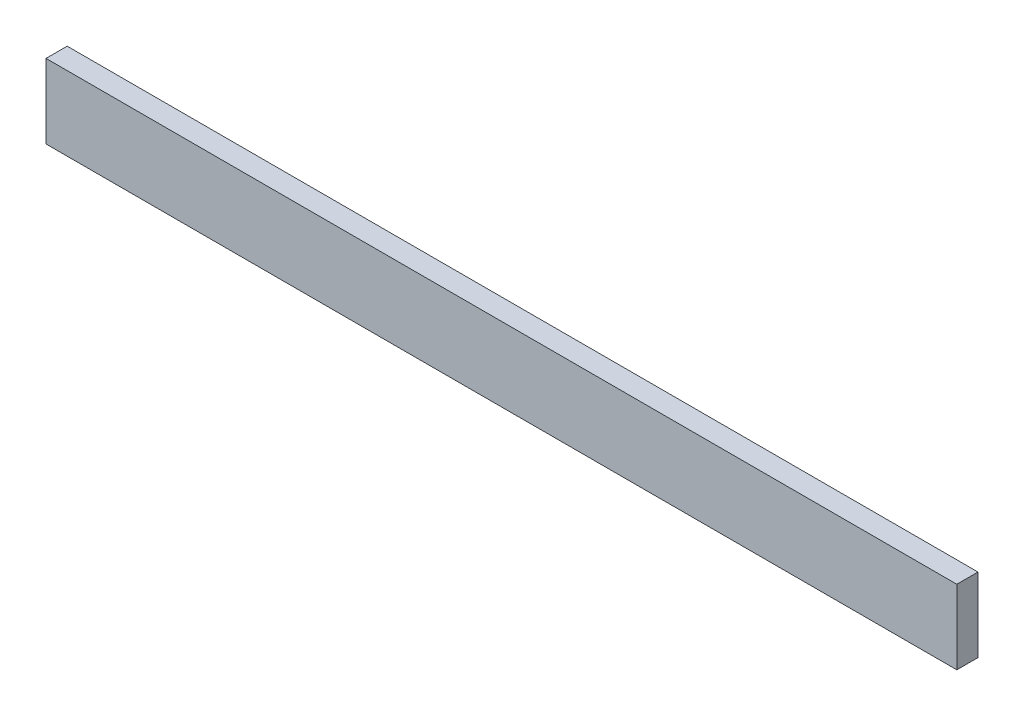
SolidWorks part; units mm, degrees
ref_plane "Front Plane" through (0, 0, 0) normal (0, 0, 1) x (1, 0, 0)
ref_plane "Top Plane" through (0, 0, 0) normal (0, 1, 0) x (1, 0, 0)
ref_plane "Right Plane" through (0, 0, 0) normal (1, 0, 0) x (0, 0, -1)
sketch "Sketch1" plane through (0, 0, 0) normal (0, 0, 1) x (1, 0, 0)
  line L1 (-86, 7) -> (86, 7)
  line L2 (-86, 7) -> (-86, -7)
  line L3 (-86, -7) -> (86, -7)
  line L4 (86, 7) -> (86, -7)
  line L5 (-86, 7) -> (86, -7) construction
  line L6 (-86, -7) -> (86, 7) construction
  point P0 (0, 0)
  dimension "D1" = 172
  dimension "D2" = 14
extrude "Boss-Extrude1" add sketch "Sketch1" against normal blind 4
